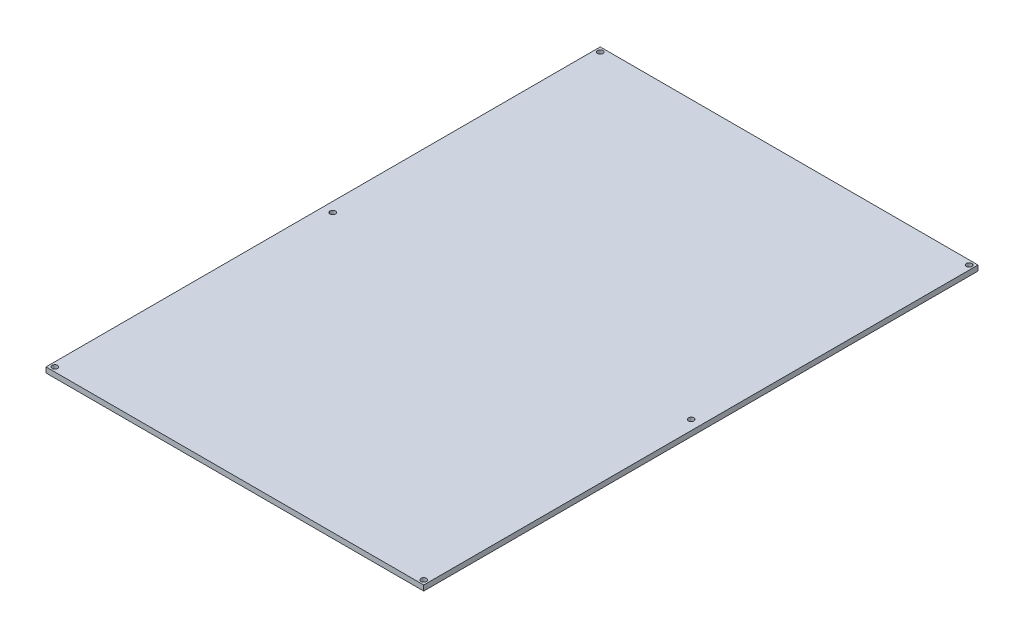
SolidWorks part; units mm, degrees
ref_plane "Alzado" through (0, 0, 0) normal (0, 0, 1) x (1, 0, 0)
ref_plane "Planta" through (0, 0, 0) normal (0, 1, 0) x (1, 0, 0)
ref_plane "Vista lateral" through (0, 0, 0) normal (1, 0, 0) x (0, 0, -1)
sketch "Croquis1" plane through (0, 0, 0) normal (0, 1, 0) x (1, 0, 0)
  line L0 (107, 314) -> (107, 0) construction
  line L1 (0, 0) -> (214, 0)
  line L2 (0, 0) -> (0, 314)
  line L3 (0, 314) -> (214, 314)
  line L4 (214, 0) -> (214, 314)
  line L5 (0, 157) -> (214, 157) construction
  circle A0 centre (2.5, 311.5) radius 1.55
  circle A1 centre (211.5, 311.5) radius 1.55
  circle A2 centre (2.5, 2.5) radius 1.55
  circle A3 centre (211.5, 2.5) radius 1.55
  circle A4 centre (5.5, 157) radius 1.55
  circle A5 centre (208.5, 157) radius 1.55
  dimension "D5" = 3.1
  dimension "D6" = 5.5
  dimension "D1" = 214
  dimension "D2" = 314
  dimension "D3" = 2.5
  dimension "D4" = 2.5
extrude "Saliente-Extruir1" add sketch "Croquis1" along normal blind 3
